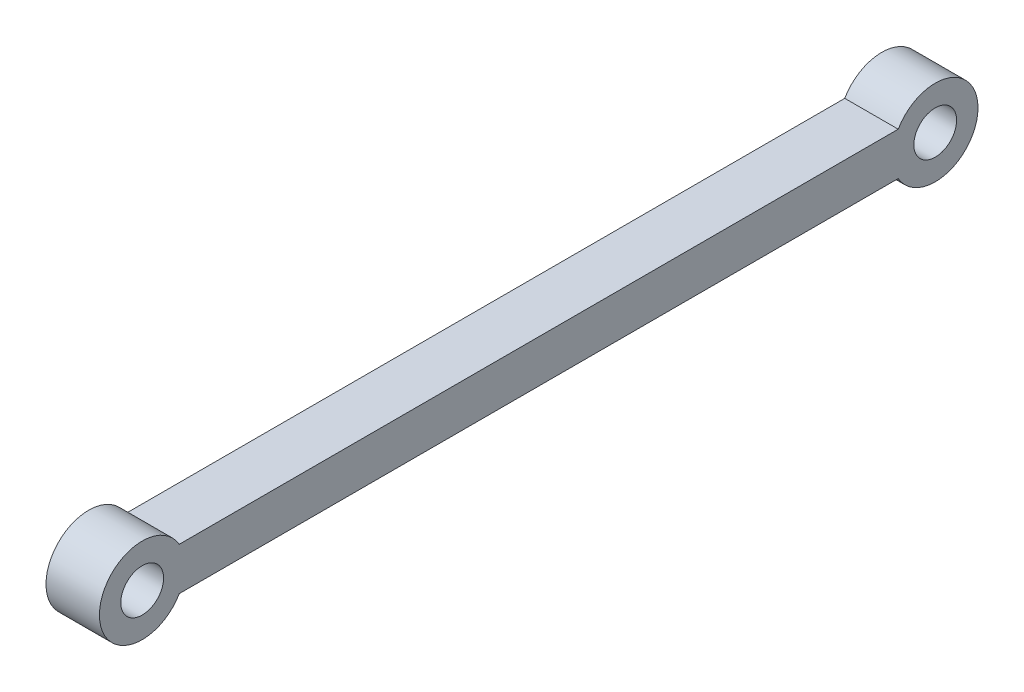
SolidWorks part; units mm, degrees
ref_plane "Front Plane" through (0, 0, 0) normal (0, 0, 1) x (1, 0, 0)
ref_plane "Top Plane" through (0, 0, 0) normal (0, 1, 0) x (1, 0, 0)
ref_plane "Right Plane" through (0, 0, 0) normal (1, 0, 0) x (0, 0, -1)
sketch "Sketch1" plane through (0, 0, 0) normal (1, 0, 0) x (0, 0, -1)
  line L0 (-16.8154, 1) -> (16.8154, 1)
  line L5 (-16.8154, -1) -> (16.8154, -1)
  line L6 (0, 1) -> (0, -1) construction
  circle A1 centre (-18.5475, 0) radius 1
  arc A2 (-16.8154, 1) -> (-16.8154, -1) centre (-18.5475, 0) ccw
  circle A4 centre (18.5475, 0) radius 1
  arc A5 (16.8154, -1) -> (16.8154, 1) centre (18.5475, 0) ccw
  point P0 (0, 0)
  point P11 (0, 1)
  point P13 (0, -1)
  point P16 (0, 0)
  dimension "D1" = 2
  dimension "D2" = 4
  dimension "D3" = 37.095
  dimension "D4" = 2
extrude "Boss-Extrude1" add sketch "Sketch1" along normal mid plane 2.5
